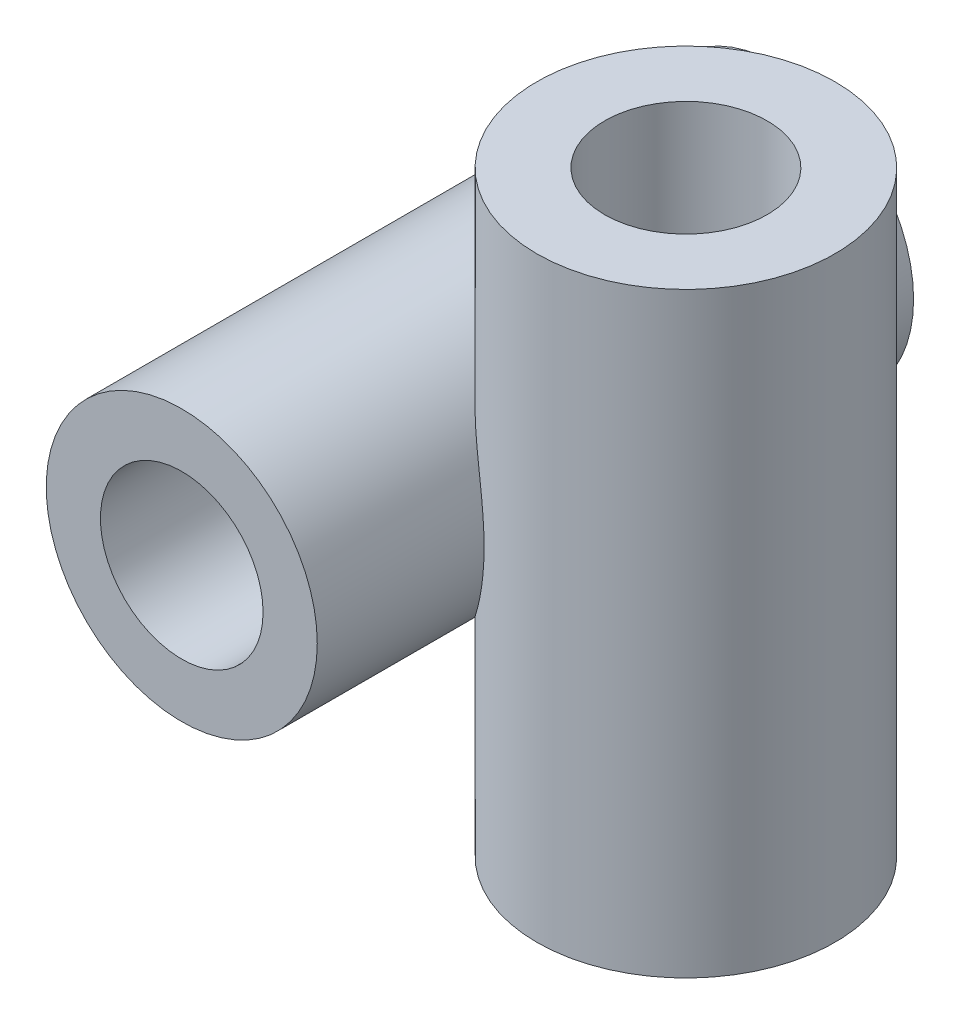
SolidWorks part; units mm, degrees
ref_plane "Front Plane" through (0, 0, 0) normal (0, 0, 1) x (1, 0, 0)
ref_plane "Top Plane" through (0, 0, 0) normal (0, 1, 0) x (1, 0, 0)
ref_plane "Right Plane" through (0, 0, 0) normal (1, 0, 0) x (0, 0, -1)
sketch "Sketch1" plane through (0, 0, 0) normal (0, 0, 1) x (1, 0, 0)
  circle A0 centre (0, 0) radius 25
  dimension "D1" = 50
extrude "Boss-Extrude1" add sketch "Sketch1" along normal blind 110
sketch "Sketch2" plane through (0, 0, 0) normal (0, 1, 0) x (1, 0, 0)
  circle A0 centre (38, -55) radius 27.5
  point P6 (0, 0)
  dimension "D1" = 55
  dimension "D2" = 38
  dimension "D3" = 55
extrude "Boss-Extrude2" add sketch "Sketch2" along normal mid plane 110
sketch "Sketch3" plane through (0, 0, 110) normal (0, 0, 1) x (1, 0, 0)
  circle A0 centre (0, 0) radius 15
  dimension "D1" = 30
extrude "Cut-Extrude1" cut sketch "Sketch3" against normal up to surface (110 mm away) up to face at (25, 0, 0)
sketch "Sketch4" plane through (0, 55, 0) normal (0, 1, 0) x (1, 0, 0)
  circle A0 centre (38, -55) radius 15
  circle A1 centre (38, -55) radius 27.5 construction
  dimension "D1" = 30
extrude "Cut-Extrude3" cut sketch "Sketch4" against normal up to surface (110 mm away) up to face at (38, -55, 82.5)
